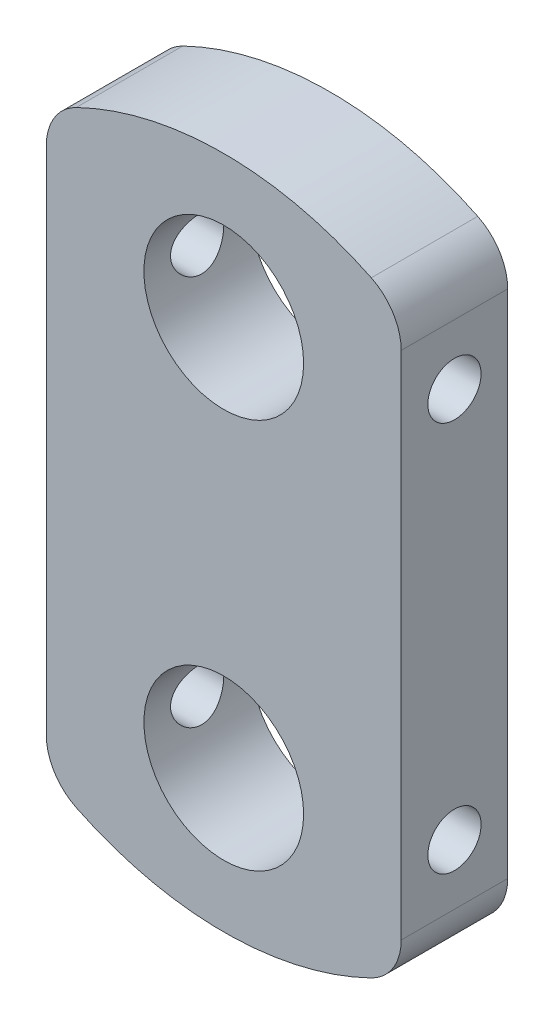
SolidWorks part; units mm, degrees
material "AISI 304"
ref_plane "Front Plane" through (0, 0, 0) normal (0, 0, 1) x (1, 0, 0)
ref_plane "Top Plane" through (0, 0, 0) normal (0, 1, 0) x (1, 0, 0)
ref_plane "Right Plane" through (0, 0, 0) normal (1, 0, 0) x (0, 0, -1)
sketch "Sketch1" plane through (0, 0, 0) normal (0, 0, 1) x (1, 0, 0)
  line L0 (0, 0) -> (10, 0)
  line L1 (0, 0) -> (-10, 0)
  line L2 (-10, 0) -> (-10, 16.1555)
  line L3 (-10, 0) -> (-10, -16.1555)
  line L4 (10, 0) -> (10, -16.1555)
  line L5 (10, 0) -> (10, 16.1555)
  circle A0 centre (0, 0) radius 19
  circle A1 centre (0, 11) radius 4.5
  circle A2 centre (0, -11) radius 4.5
  circle A3 centre (-7, -14.3875) radius 3
  circle A4 centre (7, -14.3875) radius 3
  circle A5 centre (7, 14.3875) radius 3
  circle A6 centre (-7, 14.3875) radius 3
  dimension "D1" = 10
  dimension "D2" = 38
  dimension "D4" = 11
  dimension "D5" = 9
  dimension "D7" = 10
  dimension "D3" = 10
  dimension "D6" = 11
  dimension "D8" = 10
extrude "Boss-Extrude1" add sketch "Sketch1" along normal blind 6 contours A6 L2 L1 L0 L5 A5 A0 A1 | A5 | A6 | A4 L4 L0 L1 L3 A3 A0 A2 | A3 | A4
sketch "Sketch2" plane through (10, 0, 0) normal (1, 0, 0) x (0, 0, -1)
  line L0 (0, -14.3875) -> (0, 14.3875) construction
  line L1 (0, 19) -> (-6, 19) construction
  line L2 (-6, -14.3875) -> (-6, 14.3875) construction
  circle A0 centre (-3, 11) radius 1.5
  circle A1 centre (-3, -11) radius 1.5
  dimension "D1" = 3
  dimension "D2" = 3
  dimension "D3" = 11
  dimension "D4" = 11
extrude "Cut-Extrude1" cut sketch "Sketch2" against normal through all both and the other way through all
